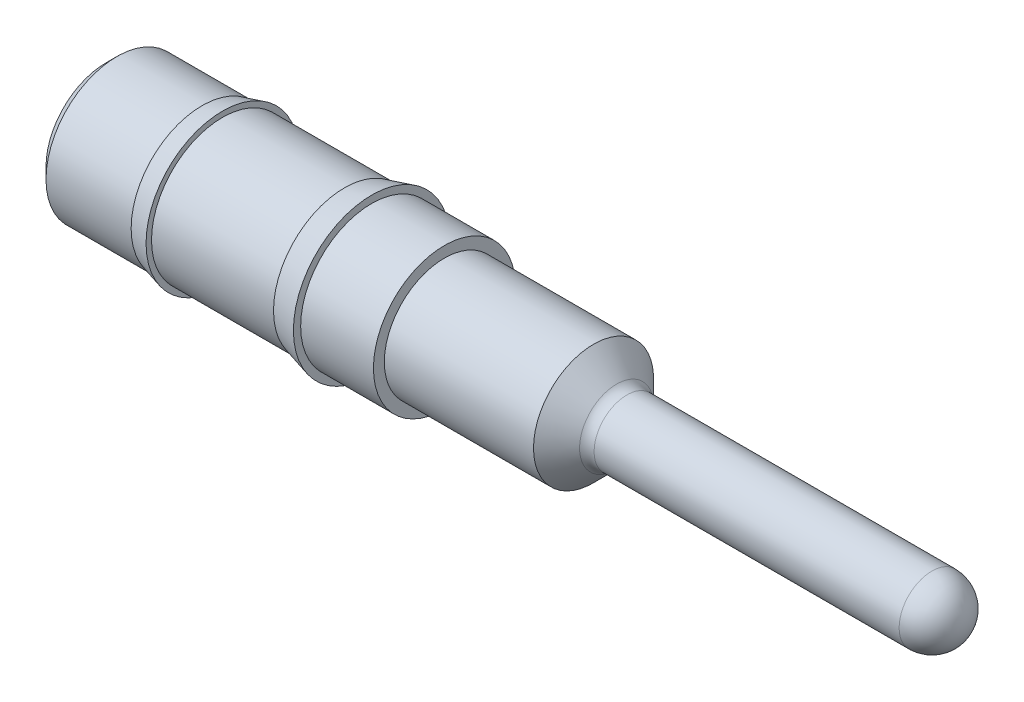
SolidWorks part; units mm, degrees
material "Brass Alloy 385"
ref_plane "Front Plane" through (0, 0, 0) normal (0, 0, 1) x (1, 0, 0)
ref_plane "Top Plane" through (0, 0, 0) normal (0, 1, 0) x (1, 0, 0)
ref_plane "Right Plane" through (0, 0, 0) normal (1, 0, 0) x (0, 0, -1)
sketch "Sketch1" plane through (0, 0, 0) normal (0, 0, 1) x (1, 0, 0)
  line L0 (0, 0) -> (0, 0.4191)
  line L1 (0, 0.4191) -> (0.0762, 0.4953)
  line L2 (0.0762, 0.4953) -> (0.6706, 0.4953)
  line L3 (0.6706, 0.4953) -> (0.8128, 0.5334)
  line L4 (0.8128, 0.5334) -> (0.8128, 0.4953)
  line L5 (0.8128, 0.4953) -> (1.6646, 0.4953)
  line L6 (1.6646, 0.4953) -> (1.8542, 0.5461)
  line L7 (1.8542, 0.5461) -> (1.8542, 0.4953)
  line L8 (1.8542, 0.4953) -> (2.3622, 0.4953)
  line L9 (2.3622, 0.4953) -> (2.3622, 0.4191)
  line L10 (2.3622, 0.4191) -> (3.4036, 0.4191)
  line L11 (3.4036, 0.4191) -> (3.5643, 0.2584)
  line L12 (3.6362, 0.2286) -> (5.7658, 0.2286)
  line L13 (0, 0) -> (5.9944, 0)
  line L14 (0, 0) -> (5.9944, 0) construction
  arc A0 (3.5643, 0.2584) -> (3.6362, 0.2286) centre (3.6362, 0.3302) ccw
  arc A1 (5.9944, 0) -> (5.7658, 0.2286) centre (5.7658, 0) ccw
revolve "RevolutionAngle1" add sketch "Sketch1" angle 360 about L14
hole_wizard "Hole1" positions "Sketch3" profile "Sketch2" legacy
sketch "Sketch3" plane through (0, 0, 0) normal (-1, 0, 0) x (0, 0, 1)
  point P0 (0, 0)
sketch "Sketch2" plane through (0, 0, 0) normal (0, 1, 0) x (0, 0, 1)
  line L0 (0, 0) -> (0, 2.3448)
  line L1 (0, 2.3448) -> (0.3937, 2.1082)
  line L2 (0.3937, 2.1082) -> (0.3937, 0)
  line L4 (0.3937, 0) -> (0, 0)
  line L6 (0, 2.3448) -> (-0.3937, 2.1082) construction
  line L7 (0, -4.2442) -> (0, 117.3081) construction
  dimension "Diameter" = 0.7874
  dimension "Depth" = 2.1082
  dimension "Drill Angle" = 118
hole_wizard "Hole2" positions "Sketch5" profile "Sketch4" legacy
sketch "Sketch5" plane through (0, 0, 0.3937) normal (-1, 0, 0) x (0, 0, 1)
  point P0 (-0.3937, 0)
sketch "Sketch4" plane through (0, 0, 0) normal (0, 1, 0) x (0, 0, 1)
  line L0 (0, 0) -> (0, 3.2159)
  line L1 (0, 3.2159) -> (0.2794, 3.048)
  line L2 (0.2794, 3.048) -> (0.2794, 0)
  line L4 (0.2794, 0) -> (0, 0)
  line L6 (0, 3.2159) -> (-0.2794, 3.048) construction
  line L7 (0, -4.2442) -> (0, 117.3081) construction
  dimension "Diameter" = 0.5588
  dimension "Depth" = 3.048
  dimension "Drill Angle" = 118
